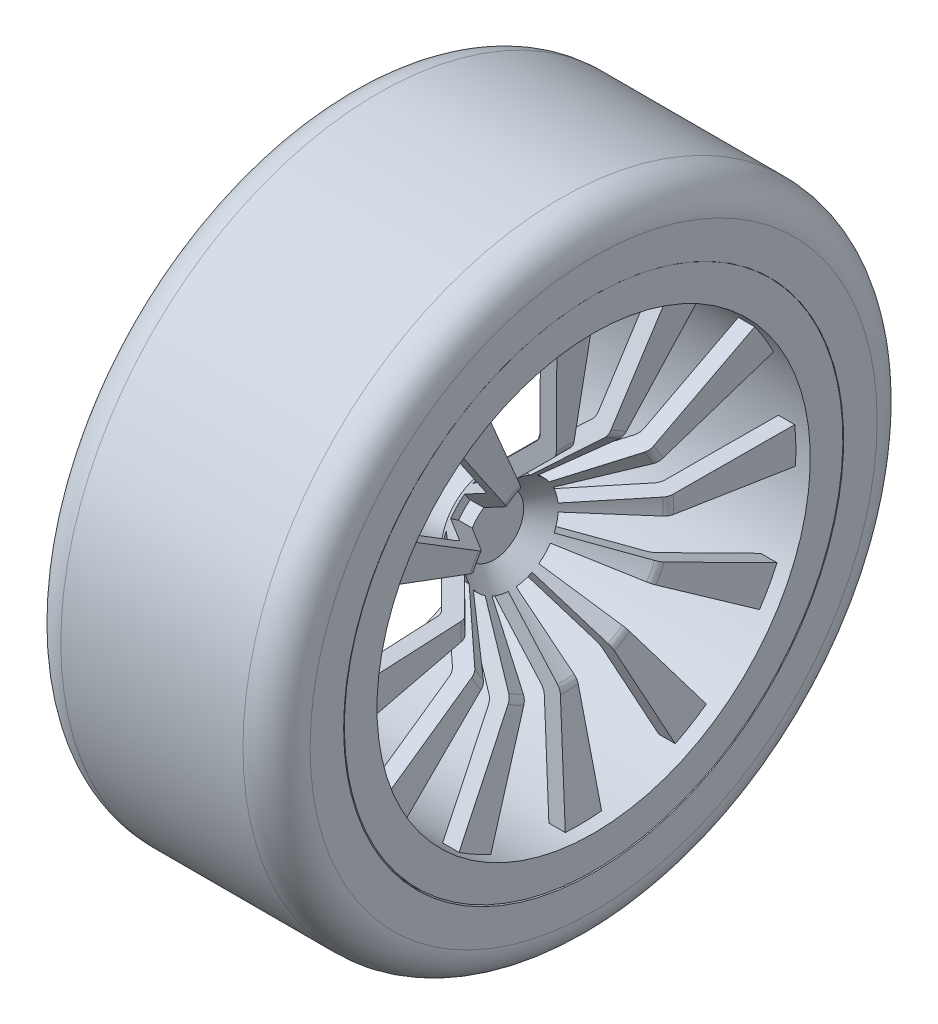
SolidWorks part; units mm, degrees
ref_plane "Front Plane" through (0, 0, 0) normal (0, 0, 1) x (1, 0, 0)
ref_plane "Top Plane" through (0, 0, 0) normal (0, 1, 0) x (1, 0, 0)
ref_plane "Right Plane" through (0, 0, 0) normal (1, 0, 0) x (0, 0, -1)
sketch "Sketch2" plane through (0, 0, 0) normal (0, 0, 1) x (1, 0, 0)
  line L0 (2.6021, -19.5) -> (2.6021, -22.6)
  line L1 (10.2013, -11.927) -> (3.2, -18.9042) construction
  line L2 (-13, 0) -> (9.79, 0)
  line L3 (-10.7, 1.7) -> (10.7, 1.7)
  line L4 (11.5, 2.5) -> (11.5, 3.4)
  line L5 (11.5, 3.4) -> (13, 3.4)
  line L6 (13, 3.4) -> (13, 0)
  line L7 (-11.5, 2.5) -> (-11.5, 3.4)
  line L8 (-11.5, 3.4) -> (-13, 3.4)
  line L9 (-13, 3.4) -> (-13, 0)
  line L10 (11.5, 0) -> (10.2013, -11.927) construction
  line L11 (13, -22.6) -> (0, -22.6) construction
  line L12 (11.5, 0) -> (10.248, -11.4984)
  line L13 (11.5, 0) -> (13, 0)
  line L14 (-5, -19.5) -> (-5, -18.2)
  line L15 (-4.5, -17.7) -> (2, -17.7)
  line L16 (-5, -19.5) -> (0, -19.5)
  line L18 (9.8959, -12.2314) -> (2.6021, -19.5)
  line L19 (8.5762, -11.1465) -> (2, -17.7) construction
  line L21 (9.79, 0) -> (8.6279, -10.6718)
  line L22 (8.238, -11.4835) -> (2, -17.7)
  line L23 (9.81, 0.184) -> (8.5762, -11.1465) construction
  line L24 (2.6021, -22.6) -> (0, -22.6)
  line L25 (0, -22.6) -> (0, -19.5)
  arc A0 (10.7, 1.7) -> (11.5, 2.5) centre (10.7, 2.5) ccw
  arc A1 (-10.7, 1.7) -> (-11.5, 2.5) centre (-10.7, 2.5) cw
  arc A2 (9.8959, -12.2314) -> (10.248, -11.4984) centre (9.0336, -11.3661) ccw
  arc A3 (8.238, -11.4835) -> (8.6279, -10.6718) centre (7.2831, -10.5253) ccw
  arc A4 (-5, -18.2) -> (-4.5, -17.7) centre (-4.5, -18.2) cw
  point P3 (0, 0)
  point P6 (0, 0)
  point P16 (0, 1.7)
  point P20 (11.5, 1.7)
  point P23 (-11.5, 1.7)
  point P27 (0, -22.6)
  point P31 (3.2, -17.7)
  dimension "D1" = 0.5
  dimension "D2" = 3.1
revolve "Revolve5" add sketch "Sketch2" angle 360 about L11
ref_plane "Plane1" through (13, 0, 0) normal (1, 0, 0) x (0, 0, -1)
sketch "Sketch4" plane through (13, 0, 0) normal (1, 0, 0) x (0, 0, -1)
  line L5 (-10.0145, -2.3399) -> (-2.1713, -18.2073)
  line L6 (-2.3286, -0.1203) -> (-0.5049, -17.7261)
  circle A1 centre (0, -22.6) radius 22.6 construction
  arc A2 (-2.3286, -0.1203) -> (-10.0145, -2.3399) centre (0, -22.6) ccw
  circle A6 centre (0, -22.6) radius 4.9 construction
  arc A7 (-0.5049, -17.7261) -> (-2.1713, -18.2073) centre (0, -22.6) ccw
  arc A8 (-0.5049, -17.7261) -> (-2.1713, -18.2073) centre (0, -22.6) ccw
  dimension "D2" = 8
extrude "Cut-Extrude4" cut sketch "Sketch4" against normal blind 10 contours A7 L6 A2 L5
pattern_circular "CirPattern1" count 12 over 360 about axis through (0, -22.6, 0) along (1, 0, 0) of "Cut-Extrude4"
sketch "Sketch6" plane through (0, 0, 0) normal (0, 0, 1) x (1, 0, 0)
  line L0 (-14.3549, -22.6776) -> (15.5188, -22.6776) construction
  line L1 (-13, 3.4) -> (-11.5, 3.4)
  line L2 (-11.5, 3.4) -> (-11.5, 2.5)
  line L3 (-11.5, 2.5) -> (-10.7, 1.7)
  line L4 (-10.7, 1.7) -> (10.7, 1.7)
  line L5 (10.7, 1.7) -> (11.5, 2.5)
  line L6 (11.5, 2.5) -> (11.5, 3.4)
  line L7 (11.5, 3.4) -> (11.5, -48.6) construction
  line L8 (11.5, 3.4) -> (13, 3.4)
  line L9 (13, -28.6) -> (13, 28.6) construction
  line L10 (13, 3.4) -> (13, 6.9)
  line L11 (9.5, 10.4) -> (-9.5, 10.4)
  line L12 (-13, 6.9) -> (-13, 3.4)
  arc A0 (-9.5, 10.4) -> (-13, 6.9) centre (-9.5, 6.9) ccw
  arc A1 (13, 6.9) -> (9.5, 10.4) centre (9.5, 6.9) ccw
  point P6 (0, 0)
  point P23 (0, 0)
  point P26 (-13, 10.4)
  point P29 (13, 10.4)
  dimension "D2" = 3.5
  dimension "D3" = 3.5
  dimension "D1" = 7
revolve "Revolve7" add sketch "Sketch6" angle 360 about L0
